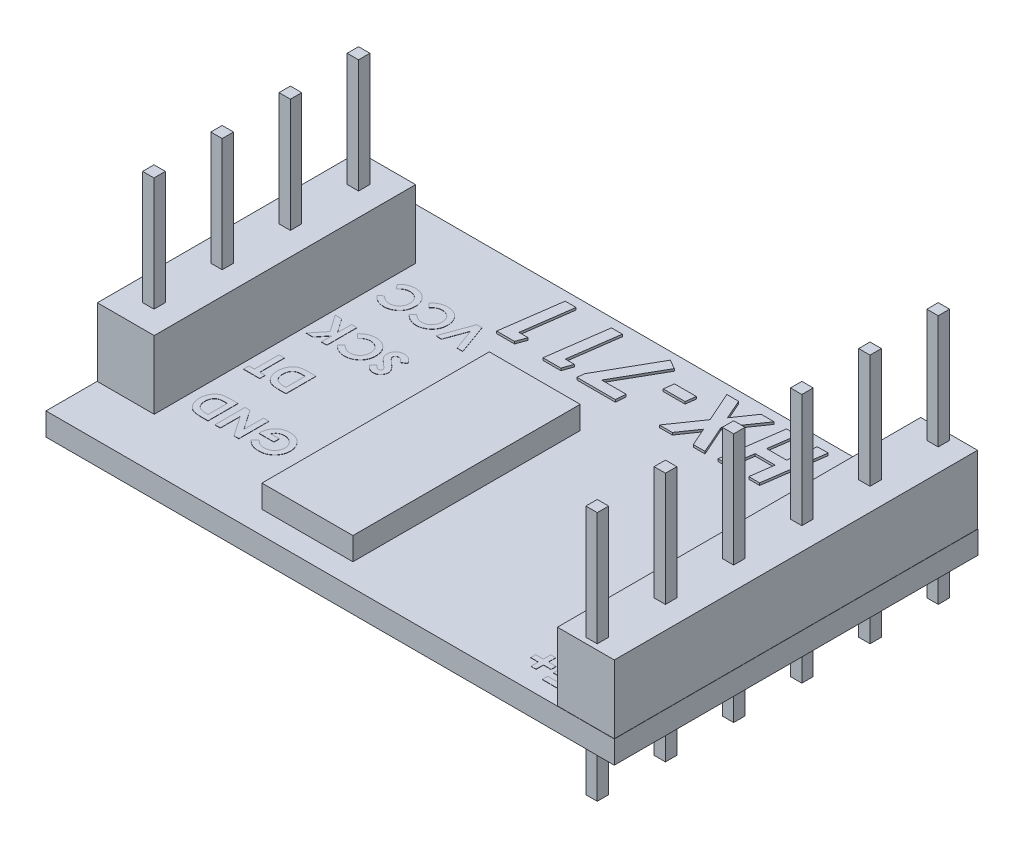
SolidWorks part; units mm, degrees
ref_plane "Front" through (0, 0, 0) normal (0, 0, 1) x (1, 0, 0)
ref_plane "Top" through (0, 0, 0) normal (0, 1, 0) x (1, 0, 0)
ref_plane "Right" through (0, 0, 0) normal (1, 0, 0) x (0, 0, -1)
sketch "Sketch1" plane through (0, 0, 0) normal (0, 1, 0) x (1, 0, 0)
  line L1 (25, -16) -> (0, -16)
  line L2 (25, -16) -> (25, 0)
  line L3 (25, 0) -> (0, 0)
  line L4 (0, -16) -> (0, 0)
  dimension "D1" = 16
  dimension "D2" = 25
extrude "Boss-Extrude1" add sketch "Sketch1" along normal blind 1
sketch "Sketch2" plane through (0, 1, 0) normal (0, 1, 0) x (1, 0, 0)
  line L0 (25, -16) -> (25, 0) construction
  line L1 (0, -16) -> (25, -16) construction
  line L2 (0, 0) -> (0, -16) construction
  point P0 (1.25, -3.5)
  point P1 (1.25, -6.5)
  point P2 (1.25, -9.5)
  point P3 (1.25, -12.5)
  point P4 (23.75, -0.5)
  point P5 (23.75, -3.5)
  point P6 (23.75, -6.5)
  point P7 (23.75, -9.5)
  point P8 (23.75, -12.5)
  point P9 (23.75, -15.5)
  dimension "D1" = 3
  dimension "D2" = 3
  dimension "D3" = 3
  dimension "D4" = 3
  dimension "D5" = 3
  dimension "D6" = 1.25
  dimension "D7" = 0.5
  dimension "D8" = 1.25
hole_wizard "Ø4.0mm Dowel Hole1" positions "3DSketch1" profile "Sketch3" hole size "Ø4.0" standard "ISO"
sketch3d "3DSketch1"
  point P0 (1.25, 1, 3.5)
  point P3 (1.25, 1, 6.5)
  point P6 (1.25, 1, 9.5)
  point P9 (1.25, 1, 12.5)
  point P12 (23.75, 1, 15.5)
  point P15 (23.75, 1, 12.5)
  point P18 (23.75, 1, 9.5)
  point P21 (23.75, 1, 6.5)
  point P24 (23.75, 1, 3.5)
  point P27 (23.75, 1, 0.5)
sketch "Sketch3" plane through (1.25, 1, 3.5) normal (1, 0, 0) x (0, 0, 1)
  line L0 (0, 0) -> (0, 15.1502)
  line L1 (0, 15.1502) -> (0.25, 15)
  line L2 (0.25, 15) -> (0.25, 0)
  line L5 (0.25, 0) -> (0, 0)
  line L10 (0, 15.1502) -> (-0.25, 15) construction
  line L11 (0, -6.35) -> (0, 107.95) construction
  dimension "Hole Dia." = 0.5
  dimension "Hole Depth" = 15
  dimension "Drill Angle" = 118
sketch "Sketch4" plane through (0, 1, 0) normal (0, 1, 0) x (1, 0, 0)
  line L0 (0, -0.5) -> (25, -0.5) construction
  line L1 (25, -16) -> (25, 0) construction
  line L2 (0, 0) -> (0, -16) construction
  line L4 (25, 0) -> (0, 0) construction
  text T0 "<b><i>HX-711</i></b>" font "Century Gothic" height in points 10
  dimension "D1" = 0.5
extrude "Boss-Extrude2" add sketch "Sketch4" along normal blind 0.1
sketch "Sketch5" plane through (0, 1, 0) normal (0, 1, 0) x (1, 0, 0)
  line L0 (25, 0) -> (0, 0) construction
  line L1 (8.5, -5) -> (12.5, -5)
  line L2 (8.5, -5) -> (8.5, -15)
  line L3 (8.5, -15) -> (12.5, -15)
  line L4 (12.5, -5) -> (12.5, -15)
  line L5 (25, -16) -> (25, 0) construction
  dimension "D1" = 4
  dimension "D2" = 10
  dimension "D3" = 5
  dimension "D4" = 12.5
extrude "Boss-Extrude3" add sketch "Sketch5" along normal blind 1
sketch "Sketch6" plane through (0, 1, 0) normal (0, 1, 0) x (1, 0, 0)
  line L0 (1, -6.25) -> (1, -6.75)
  line L1 (1, -3.25) -> (1.5, -3.25)
  line L2 (1, -3.25) -> (1, -3.75)
  line L3 (1, -3.75) -> (1.5, -3.75)
  line L4 (1.5, -3.25) -> (1.5, -3.75)
  line L5 (1, -6.75) -> (1.5, -6.75)
  line L6 (1.5, -6.25) -> (1.5, -6.75)
  line L7 (1, -6.25) -> (1.5, -6.25)
  line L8 (1, -9.25) -> (1, -9.75)
  line L9 (1, -9.75) -> (1.5, -9.75)
  line L10 (1.5, -9.25) -> (1.5, -9.75)
  line L11 (1, -9.25) -> (1.5, -9.25)
  line L12 (1, -12.25) -> (1, -12.75)
  line L13 (1, -12.75) -> (1.5, -12.75)
  line L14 (1.5, -12.25) -> (1.5, -12.75)
  line L15 (1, -12.25) -> (1.5, -12.25)
  line L17 (23.5, -3.25) -> (23.5, -3.75)
  line L18 (23.5, -0.25) -> (24, -0.25)
  line L19 (23.5, -0.25) -> (23.5, -0.75)
  line L20 (23.5, -0.75) -> (24, -0.75)
  line L21 (24, -0.25) -> (24, -0.75)
  line L22 (23.5, -3.25) -> (24, -3.25)
  line L23 (24, -3.25) -> (24, -3.75)
  line L24 (23.5, -3.75) -> (24, -3.75)
  line L25 (23.5, -6.25) -> (23.5, -6.75)
  line L26 (23.5, -6.25) -> (24, -6.25)
  line L27 (24, -6.25) -> (24, -6.75)
  line L28 (23.5, -6.75) -> (24, -6.75)
  line L29 (23.5, -9.25) -> (23.5, -9.75)
  line L30 (23.5, -9.25) -> (24, -9.25)
  line L31 (24, -9.25) -> (24, -9.75)
  line L32 (23.5, -9.75) -> (24, -9.75)
  line L33 (23.5, -12.25) -> (23.5, -12.75)
  line L34 (23.5, -12.25) -> (24, -12.25)
  line L35 (24, -12.25) -> (24, -12.75)
  line L36 (23.5, -12.75) -> (24, -12.75)
  line L37 (23.5, -15.25) -> (23.5, -15.75)
  line L38 (23.5, -15.25) -> (24, -15.25)
  line L39 (24, -15.25) -> (24, -15.75)
  line L40 (23.5, -15.75) -> (24, -15.75)
  circle A0 centre (1.25, -3.5) radius 0.25 construction
  circle A2 centre (23.75, -0.5) radius 0.25 construction
  dimension "D1" = 0.5
  dimension "D2" = 0.5
  dimension "D3" = 0.25
  dimension "D4" = 0.25
  dimension "D6" = 0.5
  dimension "D7" = 0.5
  dimension "D8" = 0.25
  dimension "D9" = 0.25
  dimension "D5" = 4
  dimension "D10" = 6
extrude "Boss-Extrude4" add sketch "Sketch6" against normal blind 3 and the other way blind 8 contours L19 L18 L21 L20 | L17 L24 L23 L22 | L25 L28 L27 L26 | L29 L32 L31 L30 | L33 L36 L35 L34 | L37 L40 L39 L38 | L12 L13 L14 L15 | L8 L9 L10 L11 | L0 L5 L6 L7 | L2 L1 L4 L3
sketch "Sketch7" plane through (0, 1, 0) normal (0, 1, 0) x (1, 0, 0)
  line L1 (24.99, -0.01) -> (22.49, -0.01)
  line L2 (24.99, -0.01) -> (24.99, -15.99)
  line L3 (24.99, -15.99) -> (22.49, -15.99)
  line L4 (22.49, -0.01) -> (22.49, -15.99)
  line L6 (0.01, -2.25) -> (2.51, -2.25)
  line L7 (0.01, -2.25) -> (0.01, -13.75)
  line L8 (0.01, -13.75) -> (2.51, -13.75)
  line L9 (2.51, -2.25) -> (2.51, -13.75)
  line L10 (1, -3.25) -> (1.5, -3.25) construction
  line L11 (1.5, -12.75) -> (1, -12.75) construction
  line L13 (25, 0) -> (0, 0) construction
  line L14 (0, -16) -> (25, -16) construction
  line L15 (0, 0) -> (0, -16) construction
  line L16 (25, -16) -> (25, 0) construction
  dimension "D1" = 2.5
  dimension "D2" = 1
  dimension "D3" = 1
  dimension "D4" = 2.5
  dimension "D5" = 0.01
  dimension "D6" = 0.01
  dimension "D7" = 0.01
  dimension "D8" = 0.01
extrude "Boss-Extrude5" add sketch "Sketch7" along normal blind 3
sketch "Sketch8" plane through (0, 1, 0) normal (0, 1, 0) x (1, 0, 0)
  line L0 (22.0186, -14) -> (20.4496, -14) construction
  line L1 (0, -16) -> (25, -16) construction
  line L2 (22.0186, -11.25) -> (20.4496, -11.25) construction
  line L3 (22.0186, -8.5) -> (20.4496, -8.5) construction
  line L4 (22.0186, -5.75) -> (20.4496, -5.75) construction
  line L5 (22.0186, -3) -> (20.4496, -3) construction
  line L6 (22.0186, -0.25) -> (20.4496, -0.25) construction
  line L7 (7.6884, -11.5) -> (2.7461, -11.5) construction
  line L8 (7.6884, -8.75) -> (2.7461, -8.75) construction
  line L9 (7.6884, -6) -> (2.7461, -6) construction
  line L10 (7.6884, -3.25) -> (2.7461, -3.25) construction
  text T0 "<b>E+</b>" font "Century Gothic" height in points 5
  text T1 "<b>E-</b>" font "Century Gothic" height in points 5
  text T2 "A-" font "Century Gothic" height in points 5
  text T3 "<b>A+</b>" font "Century Gothic" height in points 5
  text T4 "<b>B-</b>" font "Century Gothic" height in points 5
  text T5 "<b>B+</b>" font "Century Gothic" height in points 5
  text T6 "<b>GND</b>" font "Century Gothic" height in points 5
  text T7 "<b>DT</b>" font "Century Gothic" height in points 5
  text T8 "<b>SCK</b>" font "Century Gothic" height in points 5
  text T9 "<b>VCC</b>" font "Century Gothic" height in points 5
  dimension "D1" = 2
  dimension "D3" = 4
  dimension "D4" = 4.5
  dimension "D2" = 6
extrude "Boss-Extrude6" add sketch "Sketch8" along normal blind 0.01
equation "\"D2@Sketch2\"=\"D1@Sketch2\""
equation "\"D3@Sketch2\"=\"D1@Sketch2\""
equation "\"D4@Sketch2\"=\"D1@Sketch2\""
equation "\"D5@Sketch2\"=\"D1@Sketch2\""
